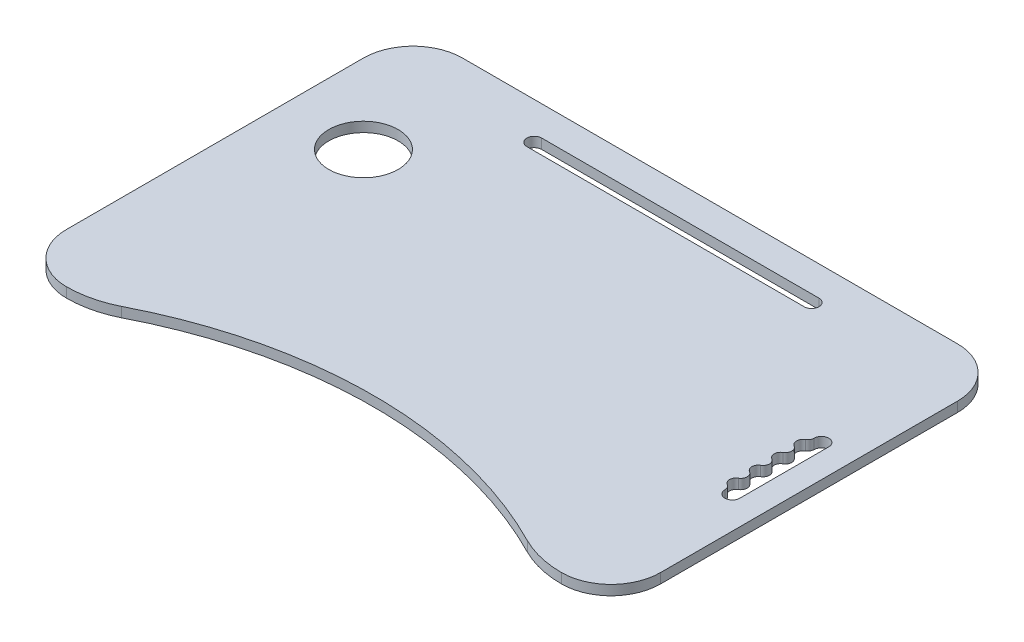
SolidWorks part; units mm, degrees
material "Balsa"
ref_plane "Front Plane" through (0, 0, 0) normal (0, 0, 1) x (1, 0, 0)
ref_plane "Top Plane" through (0, 0, 0) normal (0, 1, 0) x (1, 0, 0)
ref_plane "Right Plane" through (0, 0, 0) normal (1, 0, 0) x (0, 0, -1)
sketch "Sketch1" plane through (0, 0, 0) normal (0, 1, 0) x (1, 0, 0)
  line L0 (0, -262.766) -> (0, 262.766) construction
  line L1 (544.6809, 0) -> (-544.6809, 0) construction
  line L2 (-300, 150) -> (-300, -150)
  line L3 (-250, 200) -> (250, 200)
  line L4 (498.2968, -140) -> (-498.2968, -140) construction
  line L5 (300, 150) -> (300, -150)
  line L6 (140, 170) -> (-140, 170)
  line L7 (-140, 155) -> (140, 155)
  line L8 (275, -45) -> (275, 45)
  line L9 (260, 45) -> (260, 0) construction
  arc A0 (-300, 150) -> (-250, 200) centre (-250, 150) cw
  arc A1 (-300, -150) -> (-250, -200) centre (-250, -150) ccw
  arc A2 (-250, -200) -> (-205.0227, -189.4183) centre (-250, -99.1215) ccw
  arc A3 (-205.0227, -189.4183) -> (205.0227, -189.4183) centre (0, -590) cw
  arc A4 (250, -200) -> (205.0227, -189.4183) centre (250, -99.1215) cw
  arc A5 (300, -150) -> (250, -200) centre (250, -150) cw
  arc A6 (300, 150) -> (250, 200) centre (250, 150) ccw
  circle A7 centre (-220, 70) radius 35
  arc A8 (-140, 170) -> (-140, 155) centre (-140, 162.5) ccw
  arc A9 (140, 170) -> (140, 155) centre (140, 162.5) cw
  arc A10 (275, 45) -> (260, 45) centre (267.5, 45) ccw
  arc A11 (260, 45) -> (256.7536, 39.3812) centre (253.5144, 45) cw
  arc A12 (256.7536, 39.3812) -> (256.7536, 28.1188) centre (260, 33.75) ccw
  arc A13 (256.7536, 28.1188) -> (256.7536, 16.8812) centre (253.5144, 22.5) cw
  arc A14 (256.7536, 16.8812) -> (256.7536, 5.6188) centre (260, 11.25) ccw
  arc A15 (256.7536, 5.6188) -> (256.7536, -5.6188) centre (253.5144, 0) cw
  arc A16 (256.7536, -16.8812) -> (256.7536, -5.6188) centre (260, -11.25) cw
  arc A17 (256.7536, -28.1188) -> (256.7536, -16.8812) centre (253.5144, -22.5) ccw
  arc A18 (256.7536, -39.3812) -> (256.7536, -28.1188) centre (260, -33.75) cw
  arc A19 (260, -45) -> (256.7536, -39.3812) centre (253.5144, -45) ccw
  arc A20 (275, -45) -> (260, -45) centre (267.5, -45) cw
  point P4 (0, 0)
  point P8 (0, 0)
  point P32 (0, 200)
  point P34 (0, -140)
  point P36 (0, 155)
  point P38 (0, 170)
  point P63 (275, 0)
  dimension "D4" = 50
  dimension "D5" = 50
  dimension "D7" = 100.8785
  dimension "D8" = 450
  dimension "D10" = 70
  dimension "D17" = 45
  dimension "D18" = 6.5
  dimension "D19" = 7.5
  dimension "D1" = 300
  dimension "D2" = 400
  dimension "D3" = 200
  dimension "D6" = 90
  dimension "D9" = 140
  dimension "D11" = 130
  dimension "D12" = 80
  dimension "D13" = 15
  dimension "D14" = 30
  dimension "D15" = 140
  dimension "D16" = 25
extrude "Boss-Extrude2" add sketch "Sketch1" along normal mid plane 10
sketch "Sketch3" plane through (0, -5, 0) normal (0, -1, 0) x (-1, 0, 0)
  line L0 (416.9817, 0) -> (-416.9817, 0) construction
  line L1 (-280, -85) -> (-80, -85)
  line L2 (-80, -85) -> (-80, -70)
  line L3 (-80, -70) -> (-280, -70)
  line L4 (-280, -70) -> (-280, -85)
  line L5 (-300, -150) -> (-300, 150) construction
  line L6 (-80, 85) -> (-80, 70)
  line L7 (-280, 85) -> (-80, 85)
  line L8 (-280, 70) -> (-280, 85)
  line L9 (-80, 70) -> (-280, 70)
  point P4 (0, 0)
  dimension "D1" = 200
  dimension "D2" = 15
  dimension "D3" = 70
  dimension "D4" = 20
extrude "Boss-Extrude3" add sketch "Sketch3" along normal blind 10
sketch "Sketch5" plane through (0, 0, 70) normal (0, 0, -1) x (-1, 0, 0)
  line L0 (-280, -8) -> (-80, -8)
  line L2 (-80, -15) -> (-80, -5) construction
  line L4 (-280, -12) -> (-80, -12)
  line L5 (-280, -15) -> (-280, -5) construction
  line L6 (-280, -8) -> (-280, -12)
  line L7 (-80, -8) -> (-80, -12)
  dimension "D1" = 3
  dimension "D2" = 3
extrude "Cut-Extrude1" cut sketch "Sketch5" against normal blind 5
mirror "Mirror1" about plane through (0, 0, 0) normal (0, 0, 1) of "Cut-Extrude1"
fillet "Fillet1" radius 2 16 edges at (180, -5, 85) (80, -5, -77.5) (280, -5, -77.5) (80, -10, 85) (80, -5, 77.5) (280, -5, 77.5) (180, -5, -85) (80, -10, -85) (80, -15, -77.5) (180, -15, -85) (280, -10, -85) (280, -15, -77.5) (280, -15, 77.5) (80, -15, 77.5) (180, -15, 85) (280, -10, 85)
sketch "Sketch6" plane through (0, -5, 0) normal (0, -1, 0) x (1, 0, 0)
  line L0 (210, -125) -> (210, -135) construction
  line L1 (215, -125) -> (215, -135)
  line L2 (205, -125) -> (205, -135)
  line L3 (300, 150) -> (300, -150) construction
  line L4 (250, -200) -> (-250, -200) construction
  line L5 (115, -125) -> (115, -135) construction
  line L6 (120, -125) -> (120, -135)
  line L7 (110, -125) -> (110, -135)
  line L8 (20, -125) -> (20, -135) construction
  line L9 (25, -125) -> (25, -135)
  line L10 (15, -125) -> (15, -135)
  line L11 (-75, -125) -> (-75, -135) construction
  line L12 (-70, -125) -> (-70, -135)
  line L13 (-80, -125) -> (-80, -135)
  line L14 (-170, -125) -> (-170, -135) construction
  line L15 (-165, -125) -> (-165, -135)
  line L16 (-175, -125) -> (-175, -135)
  arc A0 (215, -125) -> (205, -125) centre (210, -125) ccw
  arc A1 (205, -135) -> (215, -135) centre (210, -135) ccw
  arc A2 (120, -125) -> (110, -125) centre (115, -125) ccw
  arc A3 (110, -135) -> (120, -135) centre (115, -135) ccw
  arc A4 (25, -125) -> (15, -125) centre (20, -125) ccw
  arc A5 (15, -135) -> (25, -135) centre (20, -135) ccw
  arc A6 (-70, -125) -> (-80, -125) centre (-75, -125) ccw
  arc A7 (-80, -135) -> (-70, -135) centre (-75, -135) ccw
  arc A8 (-165, -125) -> (-175, -125) centre (-170, -125) ccw
  arc A9 (-175, -135) -> (-165, -135) centre (-170, -135) ccw
  point P2 (210, -130)
  point P15 (115, -130)
  point P22 (20, -130)
  point P29 (-75, -130)
  point P36 (-170, -130)
  dimension "D2" = 60
  dimension "D3" = 5
  dimension "D1" = 10
  dimension "D4" = 85
  dimension "D6" = 95
  dimension "D5" = 5
extrude "Boss-Extrude4" add sketch "Sketch6" along normal blind 8
fillet "Fillet2" radius 1 40 edges at (-170, -13, -140) (-175, -13, -130) (-170, -13, -120) (-75, -13, -140) (-80, -13, -130) (-75, -13, -120) (205, -13, -130) (210, -13, -120) (215, -13, -130) (115, -13, -140) (110, -13, -130) (115, -13, -120) (15, -13, -130) (20, -13, -120) (25, -13, -130) (210, -5, -120) (215, -5, -130) (210, -5, -140) (115, -5, -120) (120, -5, -130) (115, -5, -140) (20, -5, -120) (25, -5, -130) (20, -5, -140) (-75, -5, -120) (-70, -5, -130) (-75, -5, -140) (-170, -5, -120) (-165, -5, -130) (-170, -5, -140) (-165, -13, -130) (-70, -13, -130) (210, -13, -140) (120, -13, -130) (20, -13, -140) (205, -5, -130) (110, -5, -130) (15, -5, -130) (-80, -5, -130) (-175, -5, -130)
sketch "Sketch8" plane through (-175, 0, 0) normal (-1, 0, 0) x (0, 0, 1)
  line L0 (-135, -6) -> (-125, -12) construction
  line L1 (-125, -6) -> (-135, -12) construction
  line L2 (-131.25, -11.1651) -> (-131.25, -13)
  line L3 (-125, -13) -> (-135, -13) construction
  line L4 (-131.25, -13) -> (-128.75, -13)
  line L5 (-128.75, -13) -> (-128.75, -11.1651)
  circle A0 centre (-130, -9) radius 2.5 construction
  arc A1 (-128.75, -11.1651) -> (-131.25, -11.1651) centre (-130, -9) ccw
  dimension "D1" = 5
  dimension "D2" = 2.5
  dimension "D3" = 1.8349
extrude "Cut-Extrude2" cut sketch "Sketch8" against normal through all both and the other way through all
sketch "Sketch9" plane through (0, -5, 0) normal (0, -1, 0) x (1, 0, 0)
  line L0 (-270, 156) -> (-230, 124) construction
  line L1 (-270, -124) -> (-230, -124) construction
  line L2 (-270, -124) -> (-270, -156) construction
  line L3 (-270, -156) -> (-230, -156) construction
  line L4 (-230, -124) -> (-230, -156) construction
  line L5 (-270, -124) -> (-230, -156) construction
  line L6 (-270, -156) -> (-230, -124) construction
  line L7 (-300, -150) -> (-300, 150) construction
  line L8 (-1000, 0) -> (49000, 0) construction
  line L9 (0, -1000) -> (0, 49000) construction
  line L10 (-270, 124) -> (-230, 156) construction
  line L11 (-230, 124) -> (-230, 156) construction
  line L12 (-270, 156) -> (-230, 156) construction
  line L13 (-270, 124) -> (-270, 156) construction
  line L14 (-270, 124) -> (-230, 124) construction
  circle A0 centre (-230, 124) radius 1.5
  circle A1 centre (-270, 124) radius 1.5
  circle A2 centre (-230, -156) radius 1.5
  circle A3 centre (-270, -156) radius 1.5
  circle A4 centre (-270, -124) radius 1.5
  circle A5 centre (-230, -124) radius 1.5
  circle A6 centre (-270, 156) radius 1.5
  circle A7 centre (-230, 156) radius 1.5
  circle A8 centre (230, 156) radius 1.5
  circle A9 centre (270, 156) radius 1.5
  circle A10 centre (270, 124) radius 1.5
  circle A11 centre (230, 124) radius 1.5
  circle A12 centre (230, -124) radius 1.5
  circle A13 centre (270, -124) radius 1.5
  circle A14 centre (270, -156) radius 1.5
  circle A15 centre (230, -156) radius 1.5
  point P0 (-250, -140)
  point P24 (-250, 140)
  dimension "D5" = 3
  dimension "D1" = 140
  dimension "D2" = 40
  dimension "D3" = 32
  dimension "D4" = 50
extrude "Cut-Extrude3" cut sketch "Sketch9" against normal blind 5
